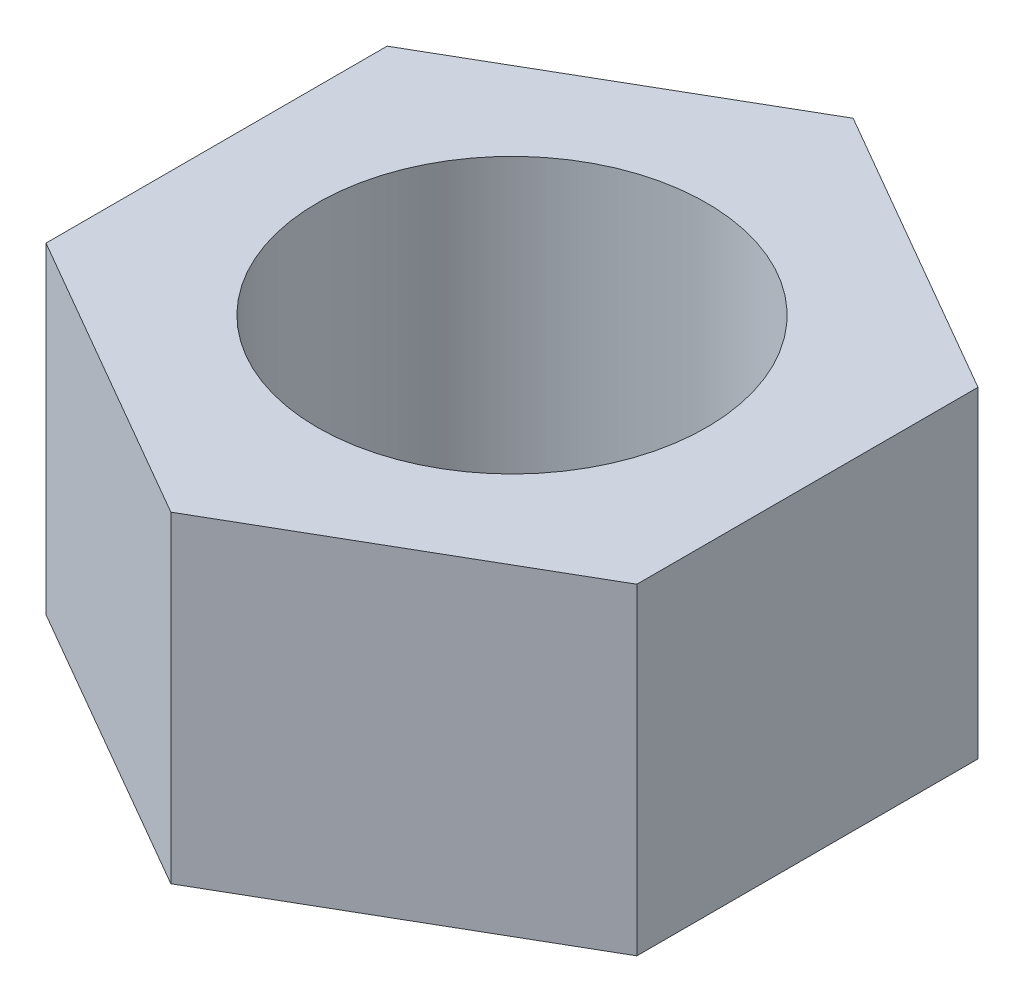
SolidWorks part; units mm, degrees
ref_plane "Front Plane" through (0, 0, 0) normal (0, 0, 1) x (1, 0, 0)
ref_plane "Top Plane" through (0, 0, 0) normal (0, 1, 0) x (1, 0, 0)
ref_plane "Right Plane" through (0, 0, 0) normal (1, 0, 0) x (0, 0, -1)
sketch "Sketch1" plane through (0, 0, 0) normal (0, 1, 0) x (1, 0, 0)
  line L1 (3.1674, -0.5285) -> (3.1674, 6.5729)
  line L2 (3.1674, 6.5729) -> (-2.9826, 10.1236)
  line L3 (-2.9826, 10.1236) -> (-9.1326, 6.5729)
  line L4 (-9.1326, 6.5729) -> (-9.1326, -0.5285)
  line L5 (-9.1326, -0.5285) -> (-2.9826, -4.0792)
  line L6 (-2.9826, -4.0792) -> (3.1674, -0.5285)
  circle A0 centre (-2.9826, 3.0222) radius 6.15 construction
  circle A1 centre (-2.9826, 3.0222) radius 4.05
  dimension "D2" = 8.1
  dimension "D1" = 12.3
extrude "Boss-Extrude1" add sketch "Sketch1" along normal blind 6.7
